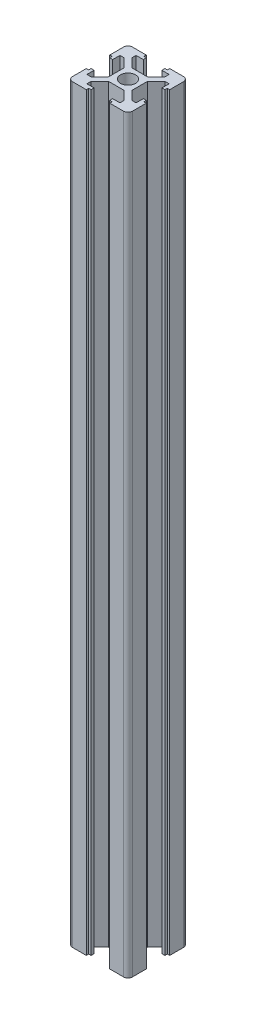
SolidWorks part; units mm, degrees
material "6063-O"
ref_plane "Front Plane" through (0, 0, 0) normal (0, 0, 1) x (1, 0, 0)
ref_plane "Top Plane" through (0, 0, 0) normal (0, 1, 0) x (1, 0, 0)
ref_plane "Right Plane" through (0, 0, 0) normal (1, 0, 0) x (0, 0, -1)
sketch "Sketch1" plane through (0, 0, 0) normal (0, 1, 0) x (1, 0, 0)
  line L0 (0, 14.5399) -> (0, 10) construction
  line L1 (-16.8658, 0) -> (2.5, 0) construction
  line L2 (13.2784, 3.9) -> (3.9, 3.9) construction
  line L3 (0, 0) -> (2.5, 0)
  line L4 (0, 0) -> (0, 2.5)
  line L5 (3.9, 10) -> (8.5, 10)
  line L6 (9.2, 0) -> (16.4291, 0) construction
  line L7 (-2.63, 3.9) -> (2.63, 3.9)
  line L9 (2.5491, 3.9) -> (2.63, 3.9)
  line L10 (3.9, 0) -> (3.9, 2.63)
  line L11 (13.2784, 3.1) -> (2.5491, 3.1) construction
  line L12 (8.2, 7.5573) -> (8.2, -3.0868) construction
  line L13 (9.2, 7.2593) -> (9.2, -8.1534) construction
  line L14 (10, 3.9) -> (9.2, 3.9)
  line L15 (9.2, 3.9) -> (9.2, 3.1)
  line L16 (9.2, 3.1) -> (8.2, 3.1)
  line L17 (8.2, 3.1) -> (8.2, 5.5)
  line L18 (8.2, 5.5) -> (6.77, 5.5)
  line L19 (6.77, 5.5) -> (3.9, 2.63)
  line L20 (5.0973, 5.5) -> (13.0082, 5.5) construction
  line L21 (3.1, 11.2046) -> (3.1, 2.6994) construction
  line L22 (3.9, 10.7498) -> (3.9, 3.9) construction
  line L23 (5.5, 11.523) -> (5.5, 1.4941) construction
  line L24 (-2.2597, 8.2) -> (6.1545, 8.2) construction
  line L25 (-2.9419, 9.2) -> (5.7225, 9.2) construction
  line L26 (3.9, 10) -> (3.9, 9.2)
  line L27 (3.9, 9.2) -> (3.1, 9.2)
  line L28 (3.1, 9.2) -> (3.1, 8.2)
  line L29 (3.1, 8.2) -> (5.5, 8.2)
  line L30 (5.5, 8.2) -> (5.5, 6.77)
  line L31 (5.5, 6.77) -> (2.63, 3.9)
  line L32 (0, 2.5) -> (0, -14.4122) construction
  line L33 (10, 3.9) -> (10, 8.5)
  line L34 (9.2, 0) -> (10, 0)
  line L35 (2.63, 3.9) -> (2.5491, 3.9) construction
  line L36 (3.9, 2.63) -> (3.9, 2.0627) construction
  line L37 (10, -3.9) -> (10, -8.5)
  line L38 (3.9, -10) -> (8.5, -10)
  line L39 (3.9, -10) -> (3.9, -9.2)
  line L40 (3.9, -9.2) -> (3.1, -9.2)
  line L41 (3.1, -9.2) -> (3.1, -8.2)
  line L42 (3.1, -8.2) -> (5.5, -8.2)
  line L43 (5.5, -8.2) -> (5.5, -6.77)
  line L44 (5.5, -6.77) -> (2.63, -3.9)
  line L45 (0, -3.9) -> (2.63, -3.9)
  line L46 (3.9, 0) -> (3.9, -2.63)
  line L47 (6.77, -5.5) -> (3.9, -2.63)
  line L48 (8.2, -5.5) -> (6.77, -5.5)
  line L49 (8.2, -3.1) -> (8.2, -5.5)
  line L50 (9.2, -3.1) -> (8.2, -3.1)
  line L51 (9.2, -3.9) -> (9.2, -3.1)
  line L52 (10, -3.9) -> (9.2, -3.9)
  line L53 (-3.9, -10) -> (-8.5, -10)
  line L54 (-10, -3.9) -> (-10, -8.5)
  line L55 (-10, -3.9) -> (-9.2, -3.9)
  line L56 (-9.2, -3.9) -> (-9.2, -3.1)
  line L57 (-9.2, -3.1) -> (-8.2, -3.1)
  line L58 (-8.2, -3.1) -> (-8.2, -5.5)
  line L59 (-8.2, -5.5) -> (-6.77, -5.5)
  line L60 (-6.77, -5.5) -> (-3.9, -2.63)
  line L61 (-3.9, 0) -> (-3.9, -2.63)
  line L62 (0, -3.9) -> (-2.63, -3.9)
  line L63 (-5.5, -6.77) -> (-2.63, -3.9)
  line L64 (-5.5, -8.2) -> (-5.5, -6.77)
  line L65 (-3.1, -8.2) -> (-5.5, -8.2)
  line L66 (-3.1, -9.2) -> (-3.1, -8.2)
  line L67 (-3.9, -9.2) -> (-3.1, -9.2)
  line L68 (-3.9, -10) -> (-3.9, -9.2)
  line L69 (-10, 3.9) -> (-10, 8.5)
  line L70 (-3.9, 10) -> (-8.5, 10)
  line L71 (-3.9, 10) -> (-3.9, 9.2)
  line L72 (-3.9, 9.2) -> (-3.1, 9.2)
  line L73 (-3.1, 9.2) -> (-3.1, 8.2)
  line L74 (-3.1, 8.2) -> (-5.5, 8.2)
  line L75 (-5.5, 8.2) -> (-5.5, 6.77)
  line L76 (-5.5, 6.77) -> (-2.63, 3.9)
  line L78 (-3.9, 0) -> (-3.9, 2.63)
  line L79 (-6.77, 5.5) -> (-3.9, 2.63)
  line L80 (-8.2, 5.5) -> (-6.77, 5.5)
  line L81 (-8.2, 3.1) -> (-8.2, 5.5)
  line L82 (-9.2, 3.1) -> (-8.2, 3.1)
  line L83 (-9.2, 3.9) -> (-9.2, 3.1)
  line L84 (-10, 3.9) -> (-9.2, 3.9)
  line L85 (0, 3.9) -> (-2.63, 3.9) [skipped]
  circle A0 centre (0, 0) radius 2.5
  arc A1 (8.5, 10) -> (10, 8.5) centre (8.5, 8.5) cw
  arc A2 (10, -8.5) -> (8.5, -10) centre (8.5, -8.5) cw
  arc A4 (-8.5, -10) -> (-10, -8.5) centre (-8.5, -8.5) cw
  arc A6 (-10, 8.5) -> (-8.5, 10) centre (-8.5, 8.5) cw
  point P12 (10, 10)
  point P126 (0, 0)
  dimension "D3" = 5
  dimension "D4" = 1.5
  dimension "D1" = 10
  dimension "D2" = 10
  dimension "D6" = 3.9
  dimension "D7" = 3.9
  dimension "D8" = 3.1
  dimension "D9" = 4
  dimension "D11" = 5.5
  dimension "D12" = 1.8
  dimension "D13" = 0.8
  dimension "D14" = 3.9
  dimension "D15" = 3.1
  dimension "D16" = 5.5
  dimension "D17" = 1.27
  dimension "D18" = 1.27
  dimension "D19" = 1.27
  dimension "D20" = 1.27
extrude "Boss-Extrude1" add sketch "Sketch1" along normal blind 250 contours A6 L69 L84 L83 L82 L81 L80 L79 L78 L61 L60 L59 L58 L57 L56 L55 L54 A4 L53 L68 L67 L66 L65 L64 L63 L62 L45 L44 L43 L42 L41 L40 L39 L38 A2 L37 L52 L51 L50 L49 L48 L47 L46 L10 L19 L18 L17 L16 L15 L14 L33
